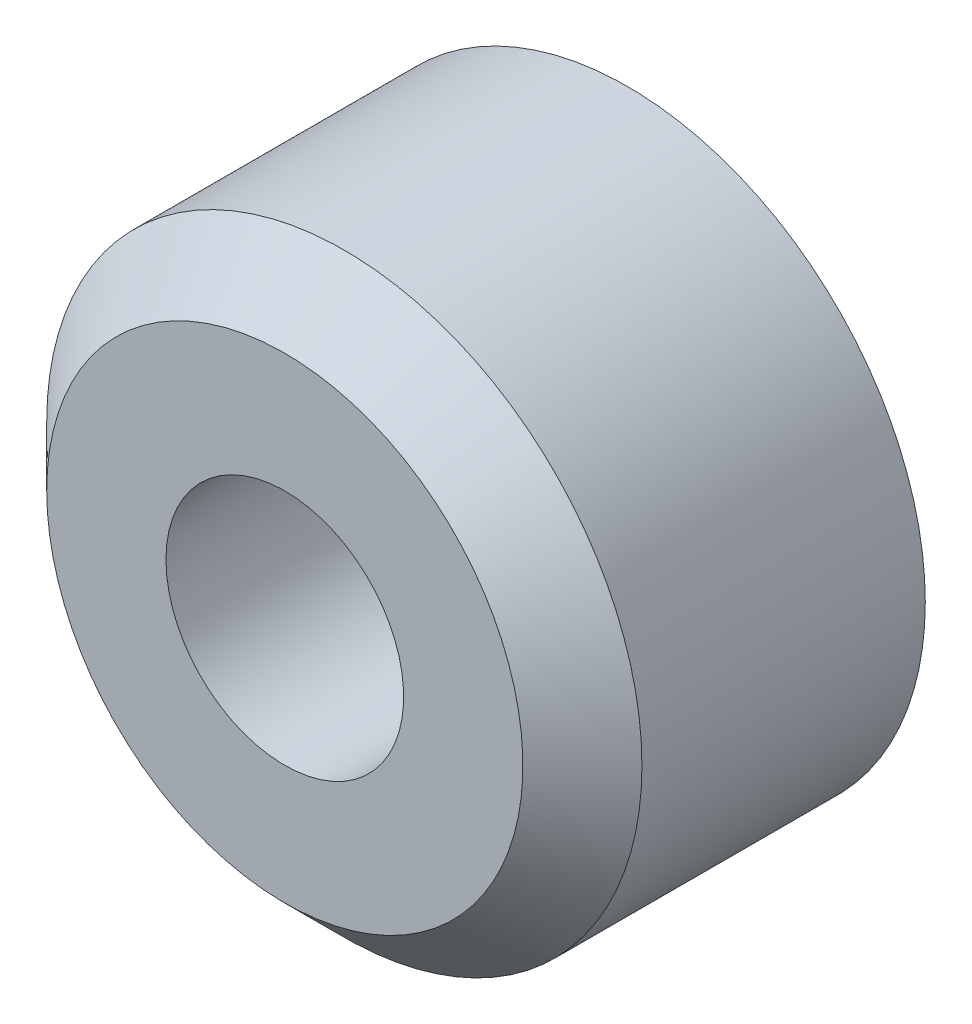
SolidWorks part; units mm, degrees
ref_plane "Front Plane" through (0, 0, 0) normal (0, 0, 1) x (1, 0, 0)
ref_plane "Top Plane" through (0, 0, 0) normal (0, 1, 0) x (1, 0, 0)
ref_plane "Right Plane" through (0, 0, 0) normal (1, 0, 0) x (0, 0, -1)
ref_plane "Plane1" through (0, 0, 0) normal (0, -1, 0) x (1, 0, 0)
sketch "Sketch1" plane through (0, 0, 0) normal (0, -1, 0) x (1, 0, 0)
  line L0 (3.9687, 3.7783) -> (3.175, 4.572)
  line L1 (3.175, 4.572) -> (1.585, 4.572)
  line L2 (1.585, 4.572) -> (1.585, 0)
  line L3 (1.585, 0) -> (3.9687, 0)
  line L4 (3.9687, 0) -> (3.9687, 3.7783)
  line L5 (0, 4.572) -> (0, 0) construction
revolve "Revolve1" add sketch "Sketch1" angle 360 about L5
